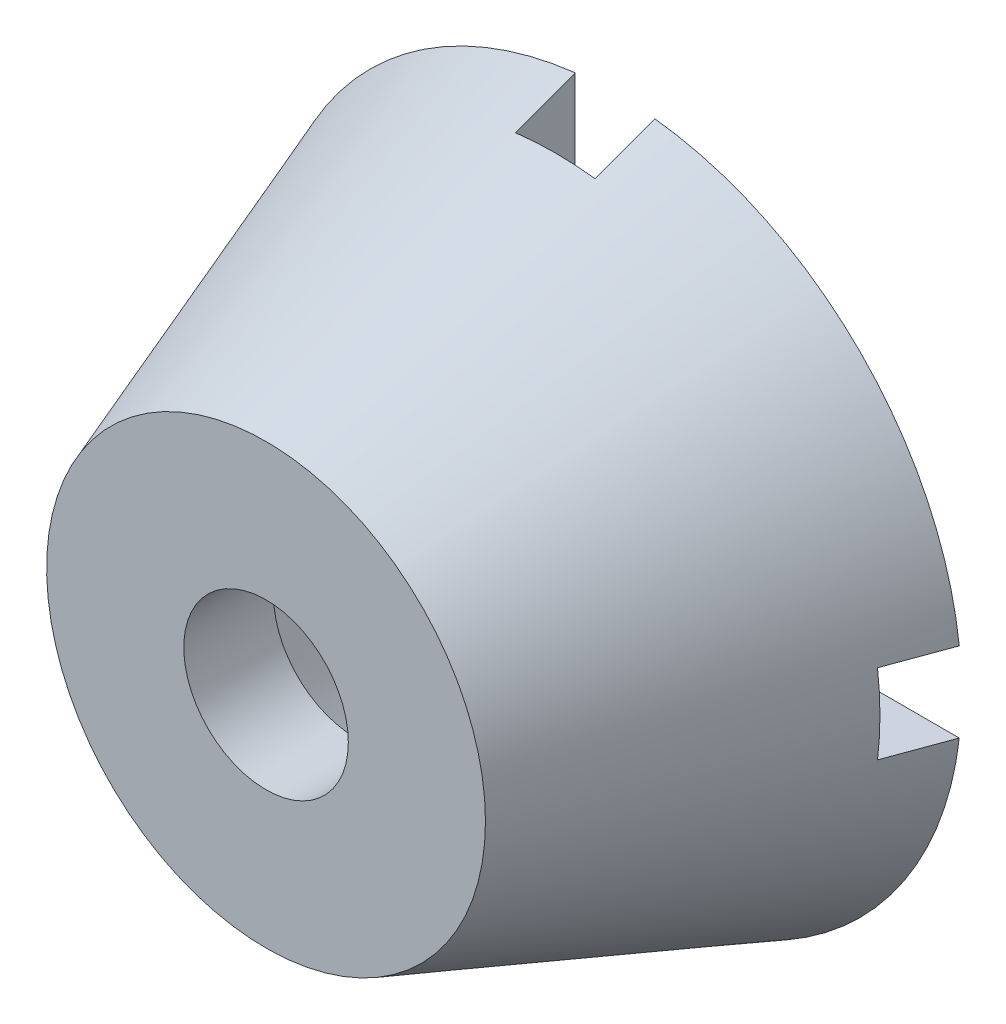
SolidWorks part; units mm, degrees
material "普通碳钢"
ref_plane "前视基准面" through (0, 0, 0) normal (0, 0, 1) x (1, 0, 0)
ref_plane "上视基准面" through (0, 0, 0) normal (0, 1, 0) x (1, 0, 0)
ref_plane "右视基准面" through (0, 0, 0) normal (1, 0, 0) x (0, 0, -1)
other "Configuration Table"
sketch "草图1" plane through (0, 0, 0) normal (0, 1, 0) x (1, 0, 0)
  line L0 (0, 0) -> (0, 35)
  line L1 (0, 35) -> (-34.739, 35)
  line L2 (-34.739, 35) -> (-22, 0)
  line L3 (-22, 0) -> (0, 0)
  line L4 (-25.1614, 35) -> (-15.6981, 9)
  line L5 (-15.6981, 9) -> (0, 9)
  dimension "D1" = 22
  dimension "D2" = 35
  dimension "D3" = 70
  dimension "D4" = 9
  dimension "D5" = 9
revolve "旋转1" add sketch "草图1" angle 360 about L0
sketch "草图2" plane through (0, 0, 0) normal (0, 0, 1) x (1, 0, 0)
  circle A0 centre (0, 0) radius 8.25
  dimension "D1" = 16.5
extrude "切除-拉伸1" cut sketch "草图2" against normal up to next
sketch "草图3" plane through (0, 0, 0) normal (0, 1, 0) x (1, 0, 0)
  line L0 (34.739, 35) -> (-34.739, 35) construction
  line L1 (-4, 29) -> (4, 29)
  line L2 (-4, 29) -> (-4, 35)
  line L3 (-4, 35) -> (4, 35)
  line L4 (4, 29) -> (4, 35)
  line L5 (-4, 29) -> (4, 35) construction
  line L6 (-4, 35) -> (4, 29) construction
  point P0 (0, 32)
  dimension "D1" = 8
  dimension "D2" = 6
extrude "切除-拉伸2" cut sketch "草图3" against normal through all and the other way through all
pattern_circular "阵列(圆周)1" count 4 over 360 about axis through (0, 0, 0) along (0, 0, 1) of "切除-拉伸2"
